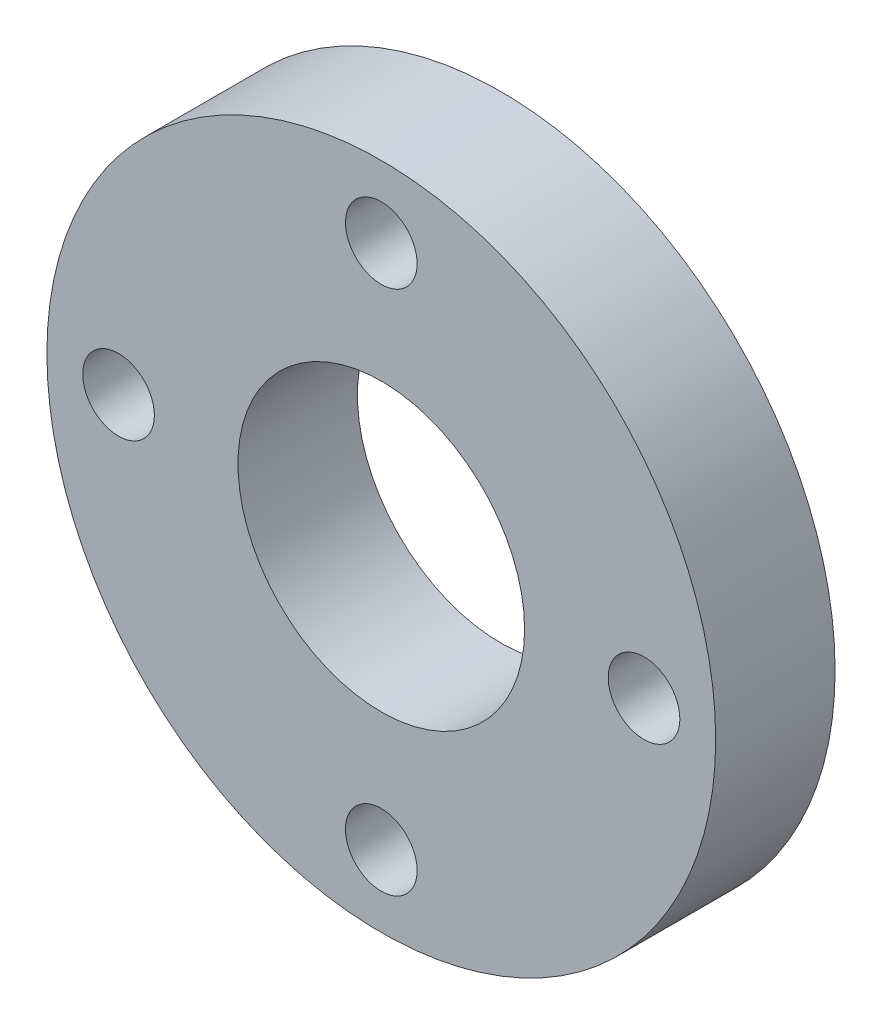
SolidWorks part; units mm, degrees
ref_plane "Alzado" through (0, 0, 0) normal (0, 0, 1) x (1, 0, 0)
ref_plane "Planta" through (0, 0, 0) normal (0, 1, 0) x (1, 0, 0)
ref_plane "Vista lateral" through (0, 0, 0) normal (1, 0, 0) x (0, 0, -1)
sketch "Croquis1" plane through (0, 0, 0) normal (0, 0, 1) x (1, 0, 0)
  line L0 (0, 0) -> (14, 0) construction
  circle A0 centre (0, 0) radius 14
  circle A1 centre (11, 0) radius 1.5
  circle A2 centre (0, -11) radius 1.5
  circle A3 centre (-11, 0) radius 1.5
  circle A4 centre (0, 11) radius 1.5
  circle A5 centre (0, 0) radius 6
  dimension "D1" = 28
  dimension "D2" = 11
  dimension "D3" = 3
  dimension "D5" = 12
  dimension "D4" = 4
extrude "Saliente-Extruir1" add sketch "Croquis1" along normal blind 5
